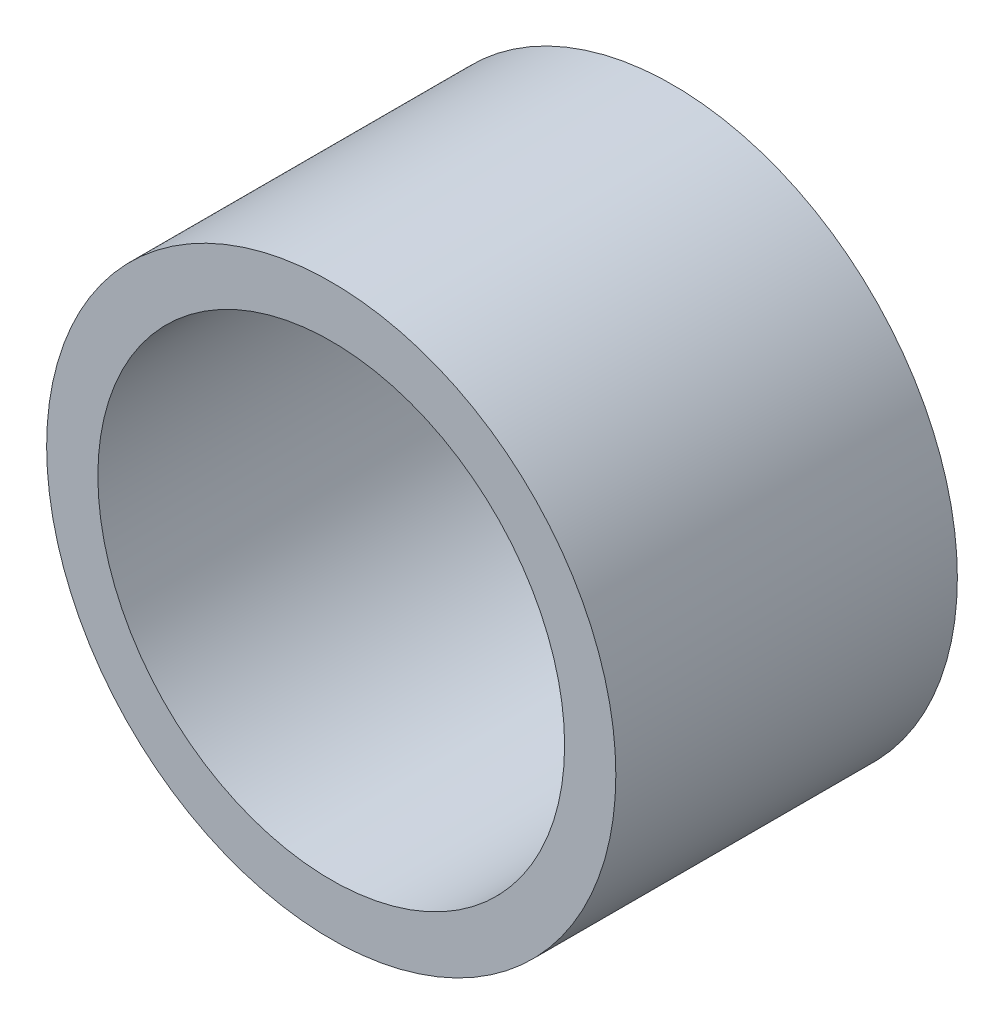
SolidWorks part; units mm, degrees
material "普通碳钢"
ref_plane "前视基准面" through (0, 0, 0) normal (0, 0, 1) x (1, 0, 0)
ref_plane "上视基准面" through (0, 0, 0) normal (0, 1, 0) x (1, 0, 0)
ref_plane "右视基准面" through (0, 0, 0) normal (1, 0, 0) x (0, 0, -1)
sketch "草图1" plane through (0, 0, 0) normal (0, 0, 1) x (1, 0, 0)
  circle A0 centre (69.8905, -10.0252) radius 25
  circle A1 centre (69.8905, -10.0252) radius 20.5
  dimension "D1" = 41
  dimension "D2" = 50
extrude "凸台-拉伸1" add sketch "草图1" along normal blind 30
